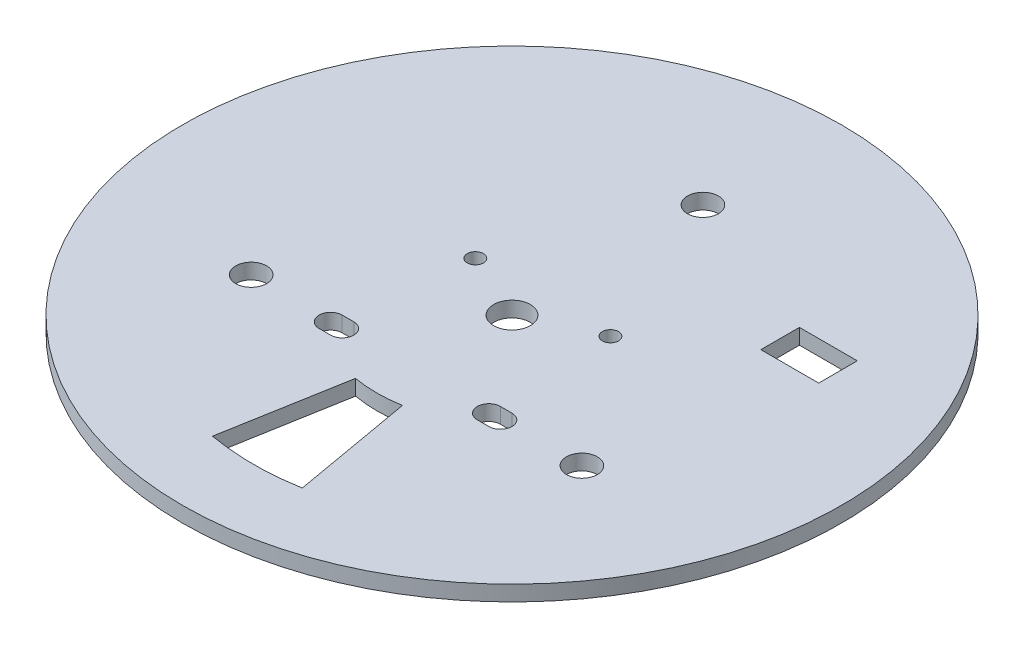
SolidWorks part; units mm, degrees
ref_plane "Plano frontal" through (0, 0, 0) normal (0, 0, 1) x (1, 0, 0)
ref_plane "Plano superior" through (0, 0, 0) normal (0, 1, 0) x (1, 0, 0)
ref_plane "Plano direito" through (0, 0, 0) normal (1, 0, 0) x (0, 0, -1)
sketch "Esboço1" plane through (0, 0, 0) normal (0, 1, 0) x (1, 0, 0)
  circle A0 centre (0, 0) radius 85.4
  dimension "D1" = 170.8
extrude "Ressalto-extrusão1" add sketch "Esboço1" along normal blind 4
sketch "Esboço3" plane through (0, 0, 0) normal (0, -1, 0) x (1, 0, 0)
  line L0 (11.9707, 32.8892) -> (22.9153, 62.9594) construction
  line L1 (-11.9707, 32.8892) -> (-22.9153, 62.9594) construction
  line L2 (6.0777, 34.4683) -> (11.6344, 65.9821)
  line L3 (0, 91.1664) -> (0, -117.3815) construction
  line L4 (-6.0777, 34.4683) -> (-11.6344, 65.9821)
  circle A1 centre (0, 0) radius 87.65
  circle A2 centre (0, 0) radius 87.65
  arc A3 (6.0777, 34.4683) -> (-6.0777, 34.4683) centre (0, 0) ccw
  arc A4 (11.6344, 65.9821) -> (-11.6344, 65.9821) centre (0, 0) ccw
  dimension "D2" = 70
  dimension "D3" = 134
  dimension "D4" = 20
  dimension "D5" = 20
  dimension "D6" = 10
  dimension "D7" = 10
  dimension "D1" = 0
extrude "Corte-extrusão2" cut sketch "Esboço3" against normal through all contours L2 A4 L4 A3
sketch "Esboço4" plane through (0, 4, 0) normal (0, 1, 0) x (1, 0, 0)
  circle A0 centre (42.8509, -24.74) radius 4
  circle A1 centre (0, 49.48) radius 4
  circle A2 centre (-42.8509, -24.74) radius 4
  point P0 (0, 49.48)
  point P2 (-42.8509, -24.74)
  point P4 (42.8509, -24.74)
extrude "Corte-extrusão3" cut sketch "Esboço4" against normal through all
sketch "Esboço5" plane through (0, 0, 0) normal (0, -1, 0) x (1, 0, 0)
  circle A1 centre (0, 0) radius 4.75
  dimension "D1" = 9.5
extrude "Corte-extrusão4" cut sketch "Esboço5" against normal through all
sketch "Esboço7" plane through (0, 4, 0) normal (0, 1, 0) x (1, 0, 0)
  line L0 (-22, -22) -> (-19, -22) construction
  line L1 (-19, -28) -> (-22, -28) construction
  line L2 (-22, -22) -> (-19, -22)
  line L3 (-19, -28) -> (-22, -28)
  line L4 (19, -28) -> (22, -28) construction
  line L5 (22, -22) -> (19, -22) construction
  line L6 (19, -28) -> (22, -28)
  line L7 (22, -22) -> (19, -22)
  arc A0 (-22, -22) -> (-22, -28) centre (-22, -25) ccw construction
  arc A1 (-19, -28) -> (-19, -22) centre (-19, -25) ccw construction
  arc A2 (-19, -28) -> (-19, -22) centre (-19, -25) ccw
  arc A3 (-22, -22) -> (-22, -28) centre (-22, -25) ccw
  arc A4 (19, -22) -> (19, -28) centre (19, -25) ccw construction
  arc A5 (22, -28) -> (22, -22) centre (22, -25) ccw construction
  arc A6 (19, -22) -> (19, -28) centre (19, -25) ccw
  arc A7 (22, -28) -> (22, -22) centre (22, -25) ccw
  circle A8 centre (-17.5, 8) radius 2.1 construction
  circle A9 centre (17.5, 8) radius 2.1 construction
  circle A10 centre (-17.5, 8) radius 2.1
  circle A11 centre (17.5, 8) radius 2.1
extrude "Corte-extrusão5" cut sketch "Esboço7" against normal through all
sketch "Esboço8" plane through (0, 4, 0) normal (0, 1, 0) x (1, 0, 0)
  line L1 (55, 34.48) -> (40, 34.48)
  line L2 (55, 34.48) -> (55, 24.48)
  line L3 (55, 24.48) -> (40, 24.48)
  line L4 (40, 34.48) -> (40, 24.48)
  circle A0 centre (0, 49.48) radius 4 construction
  dimension "D1" = 15
  dimension "D2" = 10
  dimension "D3" = 40
  dimension "D4" = 15
extrude "Corte-extrusão6" cut sketch "Esboço8" against normal up to next
